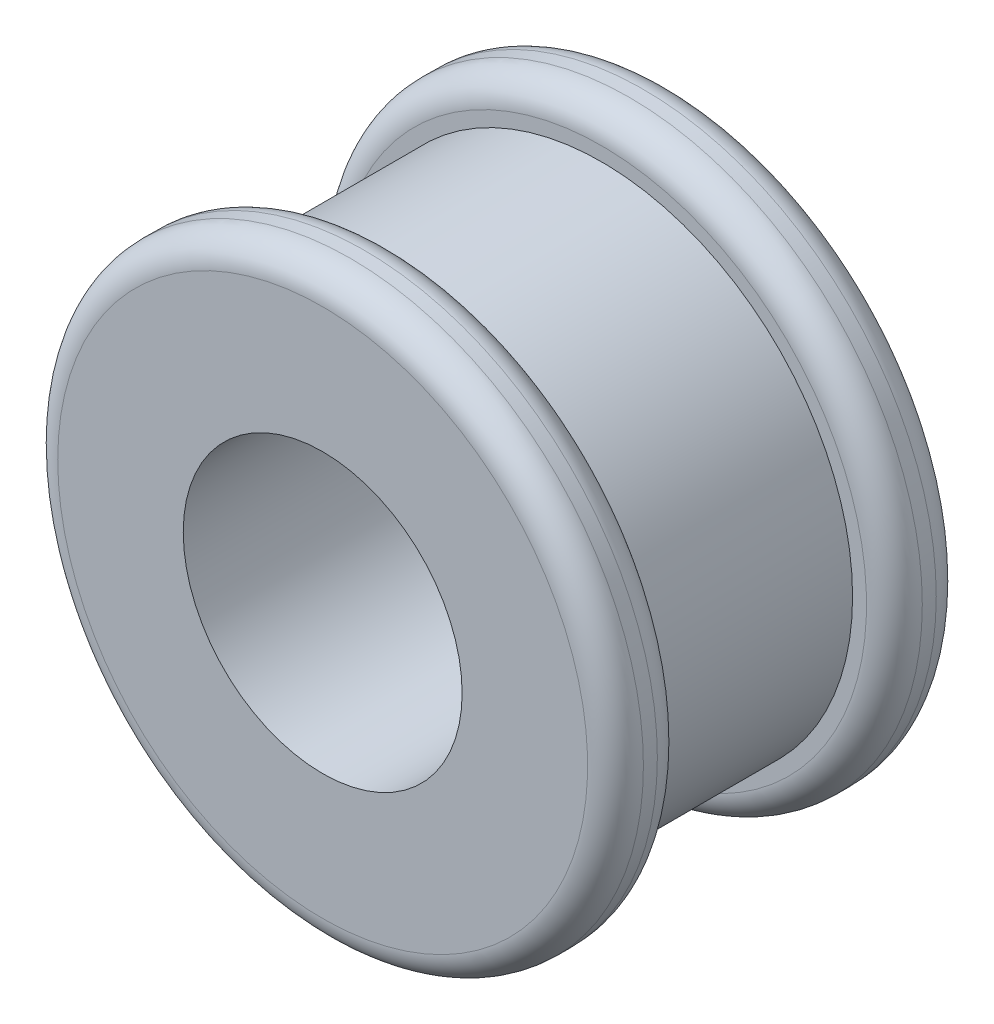
SolidWorks part; units mm, degrees
ref_plane "Front Plane" through (0, 0, 0) normal (0, 0, 1) x (1, 0, 0)
ref_plane "Top Plane" through (0, 0, 0) normal (0, 1, 0) x (1, 0, 0)
ref_plane "Right Plane" through (0, 0, 0) normal (1, 0, 0) x (0, 0, -1)
sketch "Sketch1" plane through (0, 0, 0) normal (1, 0, 0) x (0, 0, -1)
  line L0 (0, 0) -> (20.5288, 0) construction
  line L1 (0, 10) -> (25, 10)
  line L2 (25, 10) -> (25, 21)
  line L3 (25, 21) -> (20, 21)
  line L4 (20, 21) -> (20, 18)
  line L5 (20, 18) -> (5, 18)
  line L6 (5, 18) -> (5, 21)
  line L7 (5, 21) -> (0, 21)
  line L8 (0, 21) -> (0, 10)
  dimension "D1" = 5
  dimension "D2" = 5
  dimension "D3" = 15
  dimension "D4" = 21
  dimension "D5" = 3
  dimension "D6" = 10
revolve "Revolve1" add sketch "Sketch1" angle 360 about L0
fillet "Fillet1" radius 2 4 edges at (21, 0, -25) (21, 0, -20) (21, 0, -5) (21, 0, 0)
